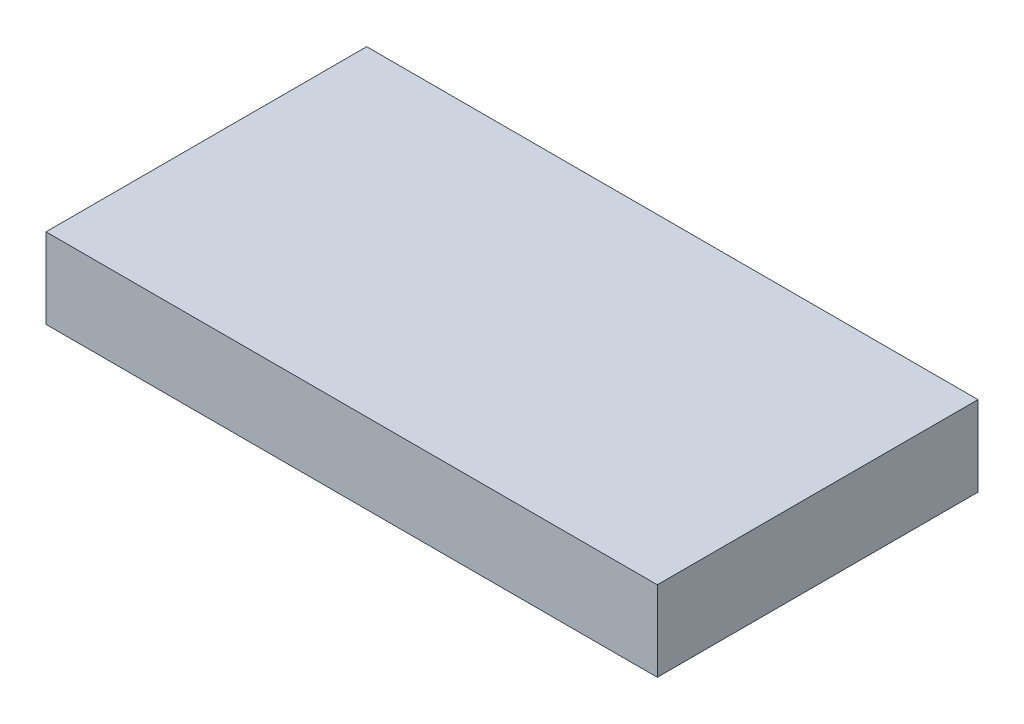
SolidWorks part; units mm, degrees
ref_plane "Front Plane" through (0, 0, 0) normal (0, 0, 1) x (1, 0, 0)
ref_plane "Top Plane" through (0, 0, 0) normal (0, 1, 0) x (1, 0, 0)
ref_plane "Right Plane" through (0, 0, 0) normal (1, 0, 0) x (0, 0, -1)
sketch "Sketch1" plane through (0, 0, 0) normal (0, 1, 0) x (1, 0, 0)
  line L1 (-96.8375, 50.8) -> (96.8375, 50.8)
  line L2 (-96.8375, 50.8) -> (-96.8375, -50.8)
  line L3 (-96.8375, -50.8) -> (96.8375, -50.8)
  line L4 (96.8375, 50.8) -> (96.8375, -50.8)
  line L5 (-96.8375, 50.8) -> (96.8375, -50.8) construction
  line L6 (-96.8375, -50.8) -> (96.8375, 50.8) construction
  point P0 (0, 0)
  dimension "D1" = 193.675
  dimension "D2" = 101.6
extrude "Boss-Extrude1" add sketch "Sketch1" along normal mid plane 25.4
sketch "Sketch2" plane through (0, -12.7, 0) normal (0, -1, 0) x (1, 0, 0)
  line L0 (0, 50.8) -> (0, -50.8) construction
  line L1 (-96.8375, 50.8) -> (96.8375, 50.8) construction
  line L2 (96.8375, -50.8) -> (-96.8375, -50.8) construction
  line L3 (-96.8375, 0) -> (96.8375, 0) construction
  line L4 (-96.8375, -50.8) -> (-96.8375, 50.8) construction
  line L5 (96.8375, 50.8) -> (96.8375, -50.8) construction
